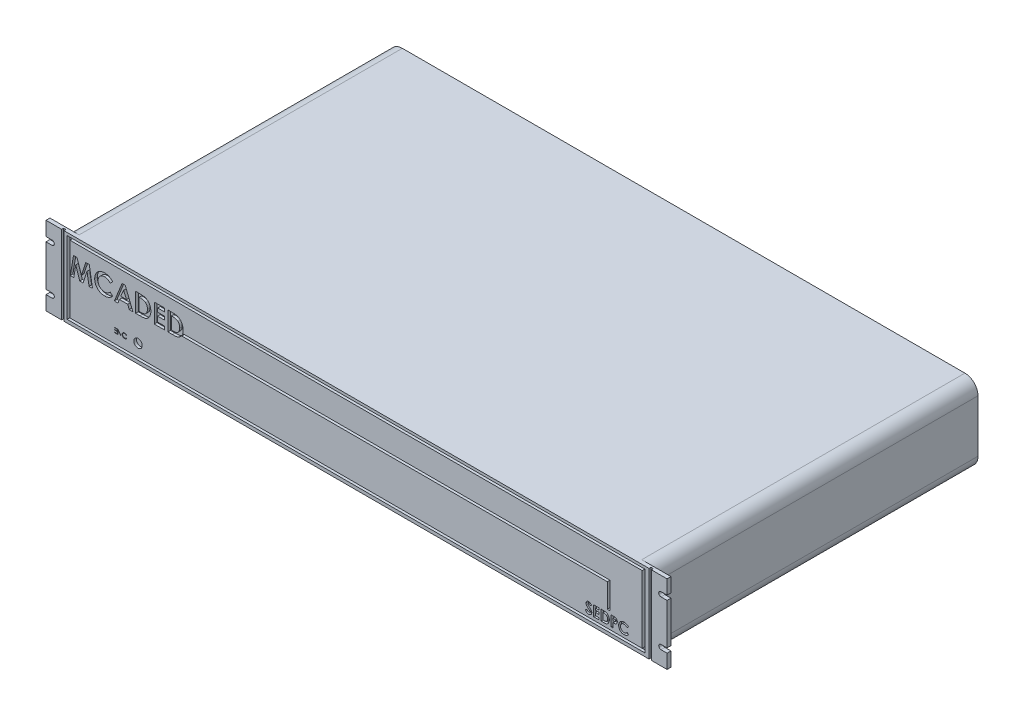
SolidWorks part; units mm, degrees
ref_plane "Alzado" through (0, 0, 0) normal (0, 0, 1) x (1, 0, 0)
ref_plane "Planta" through (0, 0, 0) normal (0, 1, 0) x (1, 0, 0)
ref_plane "Vista lateral" through (0, 0, 0) normal (1, 0, 0) x (0, 0, -1)
sketch "Croquis1" plane through (0, 0, 0) normal (0, 0, 1) x (1, 0, 0)
  line L1 (225, 30) -> (-225, 30)
  line L2 (225, 30) -> (225, -30)
  line L3 (225, -30) -> (-225, -30)
  line L4 (-225, 30) -> (-225, -30)
  line L5 (225, 30) -> (-225, -30) construction
  line L6 (225, -30) -> (-225, 30) construction
  point P0 (0, 0)
  dimension "D1" = 450
  dimension "D2" = 60
extrude "Saliente-Extruir1" add sketch "Croquis1" against normal blind 250
sketch "Croquis2" plane through (0, 0, 0) normal (0, 0, 1) x (1, 0, 0)
  line L0 (-237.3376, 19.2091) -> (-232.7031, 19.2091)
  line L1 (-225, 30) -> (-237.3376, 30)
  line L2 (-225, 30) -> (-225, -30)
  line L3 (-225, -30) -> (-237.3376, -30)
  line L4 (-237.3376, 30) -> (-237.3376, 19.2091)
  line L5 (-232.7031, 15.7347) -> (-237.3376, 15.7347)
  line L6 (-237.3376, 0) -> (-225, 0) construction
  line L7 (-232.7031, -15.7347) -> (-237.3376, -15.7347)
  line L8 (-237.3376, -19.2091) -> (-232.7031, -19.2091)
  line L9 (-237.3376, 15.7347) -> (-237.3376, -15.7347)
  line L10 (-237.3376, -19.2091) -> (-237.3376, -30)
  line L11 (0, 0) -> (0, -30) construction
  line L12 (-225, -30) -> (225, -30) construction
  line L13 (237.3376, 0) -> (225, 0) construction
  line L14 (237.3376, -19.2091) -> (237.3376, -30)
  line L15 (237.3376, 15.7347) -> (237.3376, -15.7347)
  line L16 (237.3376, -19.2091) -> (232.7031, -19.2091)
  line L17 (232.7031, -15.7347) -> (237.3376, -15.7347)
  line L18 (232.7031, 15.7347) -> (237.3376, 15.7347)
  line L19 (237.3376, 30) -> (237.3376, 19.2091)
  line L20 (225, -30) -> (237.3376, -30)
  line L21 (225, 30) -> (225, -30)
  line L22 (225, 30) -> (237.3376, 30)
  line L23 (237.3376, 19.2091) -> (232.7031, 19.2091)
  arc A0 (-232.7031, 19.2091) -> (-232.7031, 15.7347) centre (-232.7031, 17.4719) cw
  arc A1 (-232.7031, -19.2091) -> (-232.7031, -15.7347) centre (-232.7031, -17.4719) ccw
  arc A2 (232.7031, -19.2091) -> (232.7031, -15.7347) centre (232.7031, -17.4719) cw
  arc A3 (232.7031, 19.2091) -> (232.7031, 15.7347) centre (232.7031, 17.4719) ccw
extrude "Saliente-Extruir2" add sketch "Croquis2" against normal blind 3
sketch "Croquis3" plane through (0, 0, 0) normal (0, 0, 1) x (1, 0, 0)
  line L0 (237.3376, 30) -> (-237.3376, 30) construction
  line L1 (-225.3499, 30) -> (-223.5758, 30)
  line L2 (-225.3499, 30) -> (-225.3499, -30)
  line L3 (-225.3499, -30) -> (-223.5758, -30)
  line L4 (-223.5758, 30) -> (-223.5758, -30)
  line L5 (-237.3376, -30) -> (237.3376, -30) construction
  line L6 (0, 0) -> (0, -30) construction
  line L7 (223.5758, 30) -> (223.5758, -30)
  line L8 (225.3499, -30) -> (223.5758, -30)
  line L9 (225.3499, 30) -> (225.3499, -30)
  line L10 (225.3499, 30) -> (223.5758, 30)
extrude "Cortar-Extruir1" cut sketch "Croquis3" against normal blind 1.5
sketch "Croquis4" plane through (0, 0, 0) normal (0, 0, 1) x (1, 0, 0)
  line L0 (-219.1482, 25.9661) -> (-219.1482, -25.4948)
  line L1 (-221.1482, 27.9661) -> (220.3663, 27.9661)
  line L2 (-221.1482, 27.9661) -> (-221.1482, -27.4948)
  line L3 (-221.1482, -27.4948) -> (220.3663, -27.4948)
  line L4 (220.3663, 27.9661) -> (220.3663, -27.4948)
  line L5 (-219.1482, -25.4948) -> (218.3663, -25.4948)
  line L6 (218.3663, 25.9661) -> (218.3663, -25.4948)
  line L7 (-219.1482, 25.9661) -> (218.3663, 25.9661)
  dimension "D1" = 2
extrude "Cortar-Extruir2" cut sketch "Croquis4" against normal blind 2
sketch "Croquis5" plane through (0, 0, 0) normal (0, 0, 1) x (1, 0, 0)
  line L0 (-133.6024, 7.2926) -> (193.7048, 7.2926)
  line L1 (193.7048, 7.2926) -> (193.7048, -12.9409)
  line L2 (-133.6024, 5.2926) -> (191.7048, 5.2926)
  line L3 (191.7048, 5.2926) -> (191.7048, -12.9409)
  line L4 (-133.6024, 5.2926) -> (191.7048, 5.2926) construction
  line L5 (-133.6024, 7.2926) -> (-133.6024, 5.2926)
  line L6 (191.7048, -12.9409) -> (193.7048, -12.9409)
  line L7 (-212.666, 5.2926) -> (-143.0208, 5.2926) construction
  dimension "D1" = 2
extrude "Cortar-Extruir3" cut sketch "Croquis5" against normal blind 2
sketch "Croquis6" plane through (0, 0, 0) normal (0, 0, 1) x (1, 0, 0)
  line L0 (-219.1482, 2.6871) -> (-140.0076, 2.6871) construction
  line L1 (-219.1482, 25.9661) -> (-219.1482, -25.4948) construction
  text T0 "MCADED" font "Century Gothic" height in points 55
extrude "Cortar-Extruir4" cut sketch "Croquis6" against normal blind 2
sketch "Croquis7" plane through (0, 0, 0) normal (0, 0, 1) x (1, 0, 0)
  line L0 (166.0583, -23.1647) -> (216.9373, -23.1647) construction
  text T0 "SEDPC" font "Century Gothic" height in points 30
extrude "Cortar-Extruir5" cut sketch "Croquis7" against normal blind 2
sketch "Croquis8" plane through (0, 0, 0) normal (0, 0, 1) x (1, 0, 0)
  line L0 (-193.9548, -18.1332) -> (-167.0789, -18.1332) construction
  text T0 "ENC"
extrude "Cortar-Extruir6" cut sketch "Croquis8" against normal blind 2
sketch "Croquis9" plane through (0, 0, 0) normal (0, 0, 1) x (1, 0, 0)
  circle A0 centre (-167.0044, -16.2436) radius 3.2332
extrude "Cortar-Extruir7" cut sketch "Croquis9" against normal blind 2
fillet "Redondeo1" radius 10 4 edges at (225, -30, -126.5) (-225, -30, -126.5) (225, 30, -126.5) (-225, 30, -126.5)
scale "Escala1" scale about centroid uniform scaling yes scale factor 1.4
